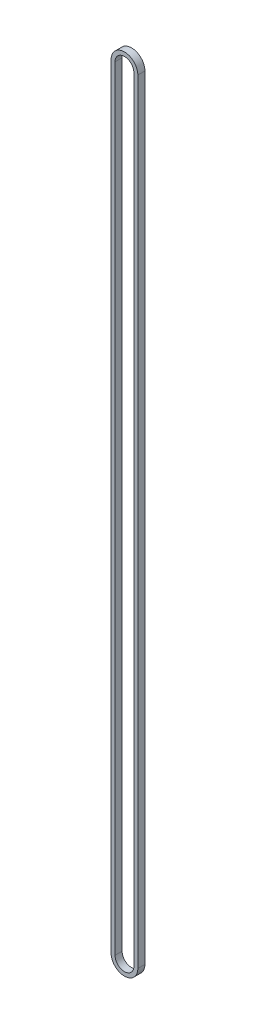
SolidWorks part; units mm, degrees
material "Найлон 6/10"
ref_plane "Спереди" through (0, 0, 0) normal (0, 0, 1) x (1, 0, 0)
ref_plane "Сверху" through (0, 0, 0) normal (0, 1, 0) x (1, 0, 0)
ref_plane "Справа" through (0, 0, 0) normal (1, 0, 0) x (0, 0, -1)
sketch "Эскиз1" plane through (0, 0, 0) normal (0, 0, 1) x (1, 0, 0)
  line L0 (0, -245.925) -> (0, 245.925) construction
  line L1 (-8.5, -245.925) -> (-8.5, 245.925)
  line L2 (8.5, -245.925) -> (8.5, 245.925)
  line L3 (0, -245.925) -> (0, 245.925) construction
  line L4 (-6, -245.925) -> (-6, 245.925)
  line L5 (6, -245.925) -> (6, 245.925)
  arc A0 (-8.5, -245.925) -> (8.5, -245.925) centre (0, -245.925) ccw
  arc A1 (8.5, 245.925) -> (-8.5, 245.925) centre (0, 245.925) ccw
  arc A2 (-6, -245.925) -> (6, -245.925) centre (0, -245.925) ccw
  arc A3 (6, 245.925) -> (-6, 245.925) centre (0, 245.925) ccw
  point P3 (0, 0)
  point P10 (0, 0)
  dimension "D1" = 491.85
  dimension "D2" = 17
  dimension "D3" = 2.5
extrude "Бобышка-Вытянуть1" add sketch "Эскиз1" along normal blind 4.5
